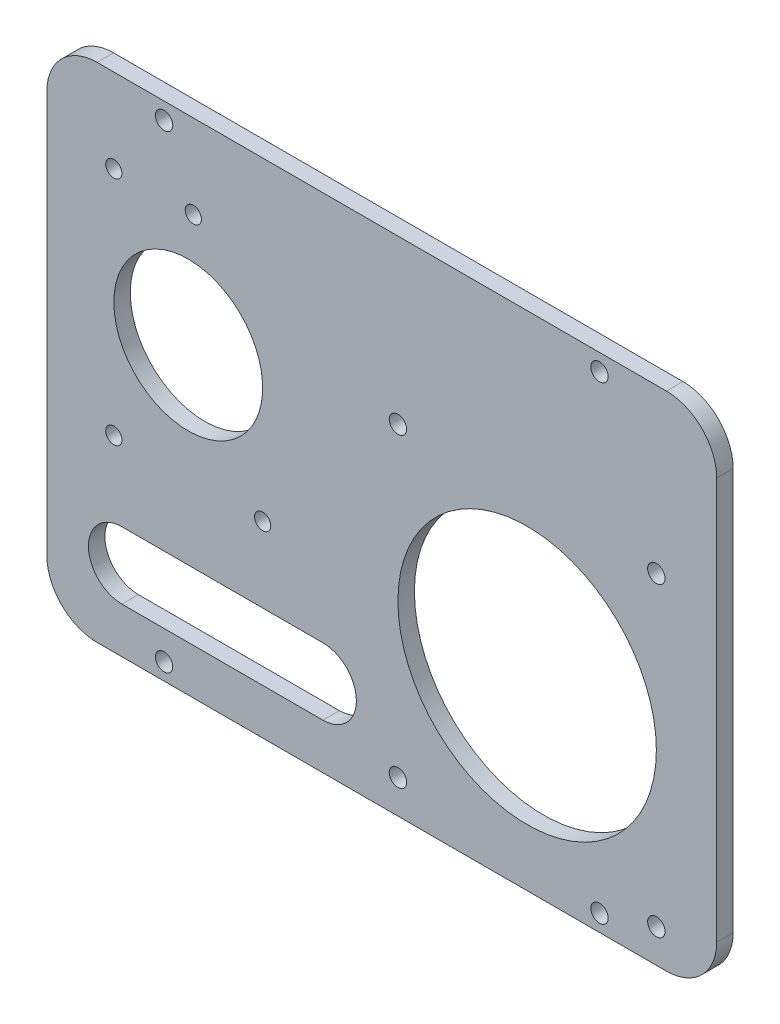
SolidWorks part; units mm, degrees
ref_plane "Alzado" through (0, 0, 0) normal (0, 0, 1) x (1, 0, 0)
ref_plane "Planta" through (0, 0, 0) normal (0, 1, 0) x (1, 0, 0)
ref_plane "Vista lateral" through (0, 0, 0) normal (1, 0, 0) x (0, 0, -1)
sketch "Croquis1" plane through (0, 0, 0) normal (0, 0, 1) x (1, 0, 0)
  line L1 (-53.975, -47.625) -> (53.975, -47.625)
  line L2 (-63.5, -38.1) -> (-63.5, 38.1)
  line L3 (-53.975, 47.625) -> (53.975, 47.625)
  line L4 (63.5, -38.1) -> (63.5, 38.1)
  line L5 (-63.5, -47.625) -> (63.5, 47.625) construction
  line L6 (-63.5, 47.625) -> (63.5, -47.625) construction
  arc A0 (-53.975, -47.625) -> (-63.5, -38.1) centre (-53.975, -38.1) cw
  arc A1 (53.975, -47.625) -> (63.5, -38.1) centre (53.975, -38.1) ccw
  arc A2 (53.975, 47.625) -> (63.5, 38.1) centre (53.975, 38.1) cw
  arc A3 (-63.5, 38.1) -> (-53.975, 47.625) centre (-53.975, 38.1) cw
  point P0 (0, 0)
  dimension "D3" = 9.525
  dimension "D1" = 127
  dimension "D2" = 95.25
extrude "Saliente-Extruir1" add sketch "Croquis1" along normal blind 3.1242
sketch "Croquis2" plane through (0, 0, 3.1242) normal (0, 0, 1) x (1, 0, 0)
  line L1 (41.275, -44.45) -> (-41.275, -44.45)
  line L2 (41.275, -44.45) -> (41.275, 44.45)
  line L3 (41.275, 44.45) -> (-41.275, 44.45)
  line L4 (-41.275, -44.45) -> (-41.275, 44.45)
  line L5 (41.275, -44.45) -> (-41.275, 44.45) construction
  line L6 (41.275, 44.45) -> (-41.275, -44.45) construction
  line L9 (-53.975, -47.625) -> (53.975, -47.625) construction
  circle A0 centre (-41.275, 44.45) radius 1.651
  circle A1 centre (41.275, 44.45) radius 1.651
  circle A2 centre (41.275, -44.45) radius 1.651
  circle A3 centre (-41.275, -44.45) radius 1.651
  point P0 (0, 0)
  dimension "D1" = 82.55
  dimension "D3" = 3.302
  dimension "D2" = 88.9
  dimension "D4" = 3.175
extrude "Cortar-Extruir1" cut sketch "Croquis2" against normal through all contours A0 | A1 | A2 | A3
sketch "Croquis3" plane through (0, 0, 0) normal (0, 0, -1) x (-1, 0, 0)
  line L0 (-55.5625, -12.275) -> (0.4375, -12.275)
  line L1 (-52.0625, 16.725) -> (-3.0625, 16.725)
  line L2 (-52.0625, 16.725) -> (-52.0625, -41.275)
  line L3 (-52.0625, -41.275) -> (-3.0625, -41.275)
  line L4 (-3.0625, 16.725) -> (-3.0625, -41.275)
  line L5 (53.975, -47.625) -> (-53.975, -47.625) construction
  line L6 (-27.5625, -41.275) -> (-27.5625, 42.545)
  line L7 (-63.5, -38.1) -> (-63.5, 38.1) construction
  circle A0 centre (-52.0625, 16.725) radius 1.651
  circle A1 centre (-3.0625, 16.725) radius 1.651
  circle A2 centre (-3.0625, -41.275) radius 1.651
  circle A3 centre (-52.0625, -41.275) radius 1.651
  circle A4 centre (-27.5625, -12.275) radius 24.5
  point P13 (-27.5625, -12.275)
  point P14 (-3.0625, -12.275)
  point P16 (-27.5625, 16.725)
  dimension "D1" = 3.302
  dimension "D2" = 58
  dimension "D3" = 49
  dimension "D4" = 56
  dimension "D5" = 6.35
  dimension "D6" = 7.9375
  dimension "D7" = 83.82
extrude "Cortar-Extruir2" cut sketch "Croquis3" against normal blind 3.1242 contours L6 A4 L0 | L0 A4 L6 | L6 A4 L0 | L0 A4 L6 | A1 | A0 | A3 | A2
sketch "Croquis4" plane through (0, 0, 0) normal (0, 0, -1) x (-1, 0, 0)
  line L0 (50.8, 31.75) -> (50.8, -12.0396) construction
  line L1 (63.5, 38.1) -> (63.5, -38.1) construction
  line L2 (-53.975, 47.625) -> (53.975, 47.625) construction
  line L3 (11.1633, -32.6263) -> (49.2633, -32.6263) construction
  line L4 (11.1633, -26.2763) -> (49.2633, -26.2763)
  line L5 (11.1633, -38.9763) -> (49.2633, -38.9763)
  line L6 (22.5806, -12.0396) -> (50.8, -12.0396) construction
  circle A0 centre (50.8, 31.75) radius 1.5367
  circle A1 centre (35.7378, 31.75) radius 1.5367
  circle A2 centre (50.8, -12.0396) radius 1.5367
  circle A3 centre (22.5806, -12.0396) radius 1.5367
  arc A4 (11.1633, -26.2763) -> (11.1633, -38.9763) centre (11.1633, -32.6263) ccw
  arc A5 (49.2633, -38.9763) -> (49.2633, -26.2763) centre (49.2633, -32.6263) ccw
  circle A6 centre (36.6903, 9.8552) radius 14.1097
  point P8 (50.8, 30.2133)
  point P9 (50.8, -10.5029)
  point P10 (24.1173, -12.0396)
  point P11 (49.2633, -12.0396)
  point P12 (37.2745, 31.75)
  point P13 (49.2633, 31.75)
  point P14 (50.8, 9.8552)
  point P18 (30.2133, -32.6263)
  point P27 (0, 0)
  point P29 (36.6903, -12.0396)
  point P31 (50.8, -13.5763)
  point P32 (0, 0)
  dimension "D1" = 40.7162
  dimension "D4" = 3.0734
  dimension "D5" = 12.7
  dimension "D8" = 6.35
  dimension "D2" = 25.146
  dimension "D3" = 11.9888
  dimension "D6" = 15.875
  dimension "D7" = 12.7
  dimension "D9" = 38.1
extrude "Cortar-Extruir3" cut sketch "Croquis4" against normal through all contours A6 | A1 | A0 | A2 | A3 | L4 A5 L5 A4
